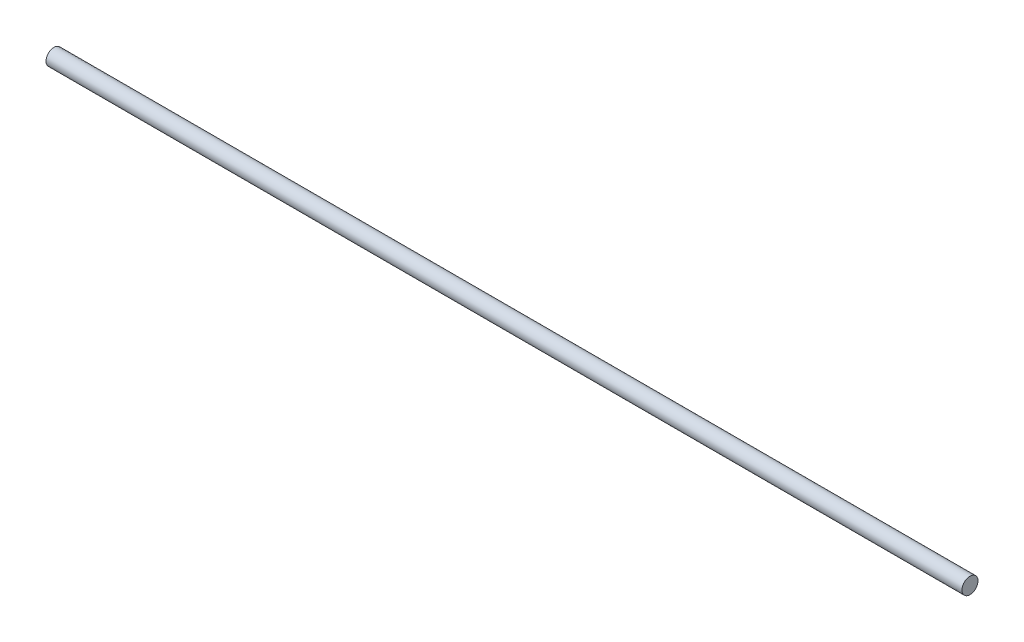
SolidWorks part; units mm, degrees
ref_plane "Front Plane" through (0, 0, 0) normal (0, 0, 1) x (1, 0, 0)
ref_plane "Top Plane" through (0, 0, 0) normal (0, 1, 0) x (1, 0, 0)
ref_plane "Right Plane" through (0, 0, 0) normal (1, 0, 0) x (0, 0, -1)
sketch "Sketch1" plane through (0, 0, 0) normal (1, 0, 0) x (0, 0, -1)
  circle A0 centre (0, 0) radius 1.778
  dimension "D1" = 3.556
extrude "Boss-Extrude1" add sketch "Sketch1" along normal mid plane 203.2
equation "\"HingeLength\"=8"
equation "\"D1@Boss-Extrude1\"=\"HingeLength\""
